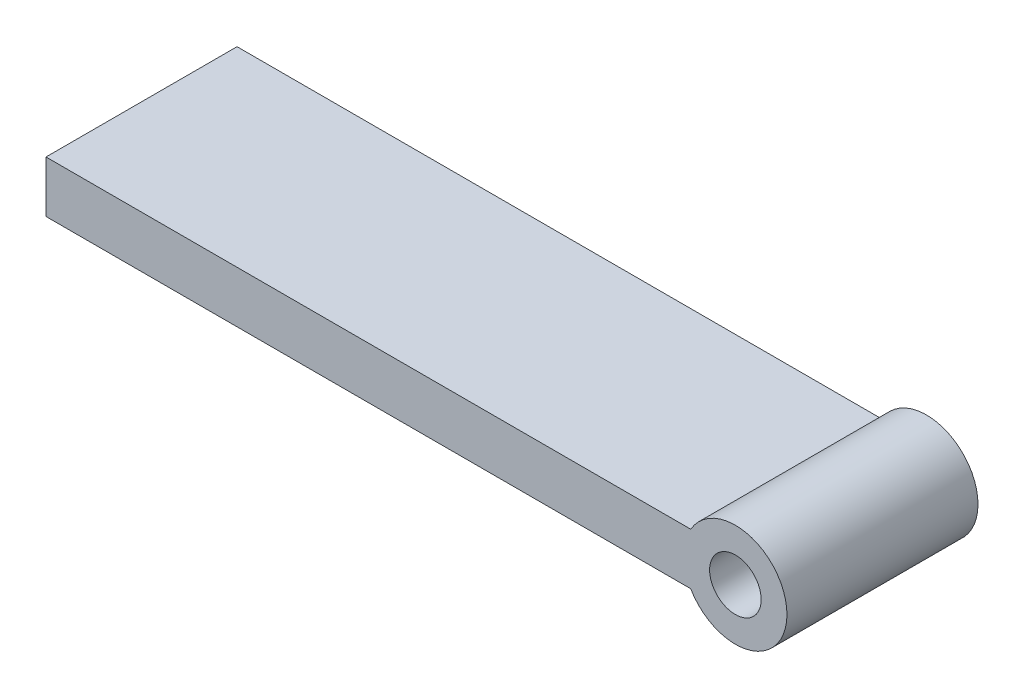
SolidWorks part; units mm, degrees
ref_plane "Front Plane" through (0, 0, 0) normal (0, 0, 1) x (1, 0, 0)
ref_plane "Top Plane" through (0, 0, 0) normal (0, 1, 0) x (1, 0, 0)
ref_plane "Right Plane" through (0, 0, 0) normal (1, 0, 0) x (0, 0, -1)
sketch "Sketch1" plane through (0, 0, 0) normal (0, 0, 1) x (1, 0, 0)
  line L0 (0, 0) -> (0, 6)
  line L1 (0, 6) -> (75.0038, 6)
  line L2 (0, 0) -> (75.0038, 0)
  arc A1 (75.0038, 0) -> (75.0038, 6) centre (80.2, 3) ccw
  circle A2 centre (80.2, 3) radius 3
  dimension "D2" = 6
extrude "Boss-Extrude1" add sketch "Sketch1" along normal blind 22.225
